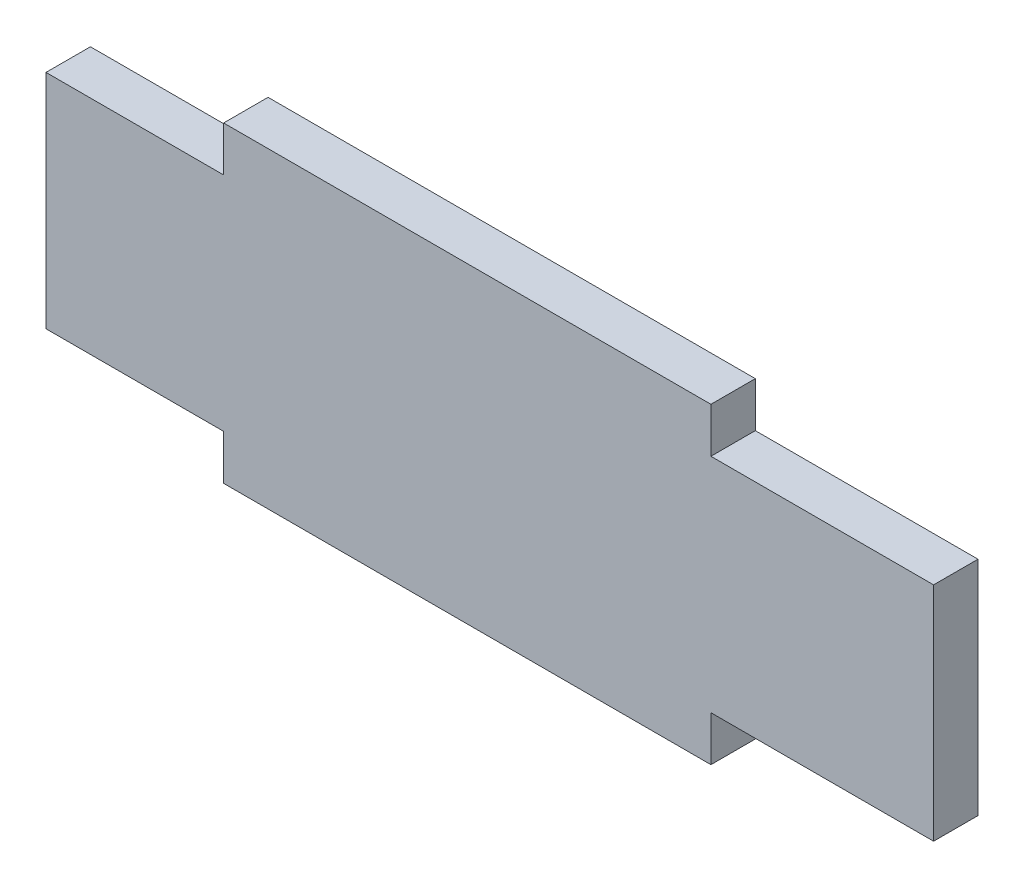
SolidWorks part; units mm, degrees
ref_plane "正面" through (0, 0, 0) normal (0, 0, 1) x (1, 0, 0)
ref_plane "平面" through (0, 0, 0) normal (0, 1, 0) x (1, 0, 0)
ref_plane "右側面" through (0, 0, 0) normal (1, 0, 0) x (0, 0, -1)
sketch "ｽｹｯﾁ1" plane through (0, 0, 0) normal (0, 0, 1) x (1, 0, 0)
  line L0 (99.93, 12.5) -> (177.1233, 12.5) construction
  line L1 (0, 0) -> (99.93, 0)
  line L2 (0, 0) -> (0, 25)
  line L3 (0, 25) -> (99.93, 25)
  line L4 (99.93, 0) -> (99.93, 25)
  line L5 (74.86, 25) -> (20, 25)
  line L6 (74.86, 25) -> (74.86, 30.07)
  line L7 (74.86, 30.07) -> (20, 30.07)
  line L8 (20, 25) -> (20, 30.07)
  line L9 (74.86, -5.07) -> (20, -5.07)
  line L10 (20, 0) -> (20, -5.07)
  line L11 (74.86, 0) -> (20, 0)
  line L12 (74.86, 0) -> (74.86, -5.07)
  line L13 (47.43, -5.07) -> (47.43, 14.4644) construction
  point P9 (20, 27.535)
  dimension "D1" = 99.93
  dimension "D2" = 25
  dimension "D3" = 5.07
  dimension "D4" = 25.07
  dimension "D5" = 20
extrude "ﾎﾞｽ - 押し出し1" add sketch "ｽｹｯﾁ1" along normal blind 5
